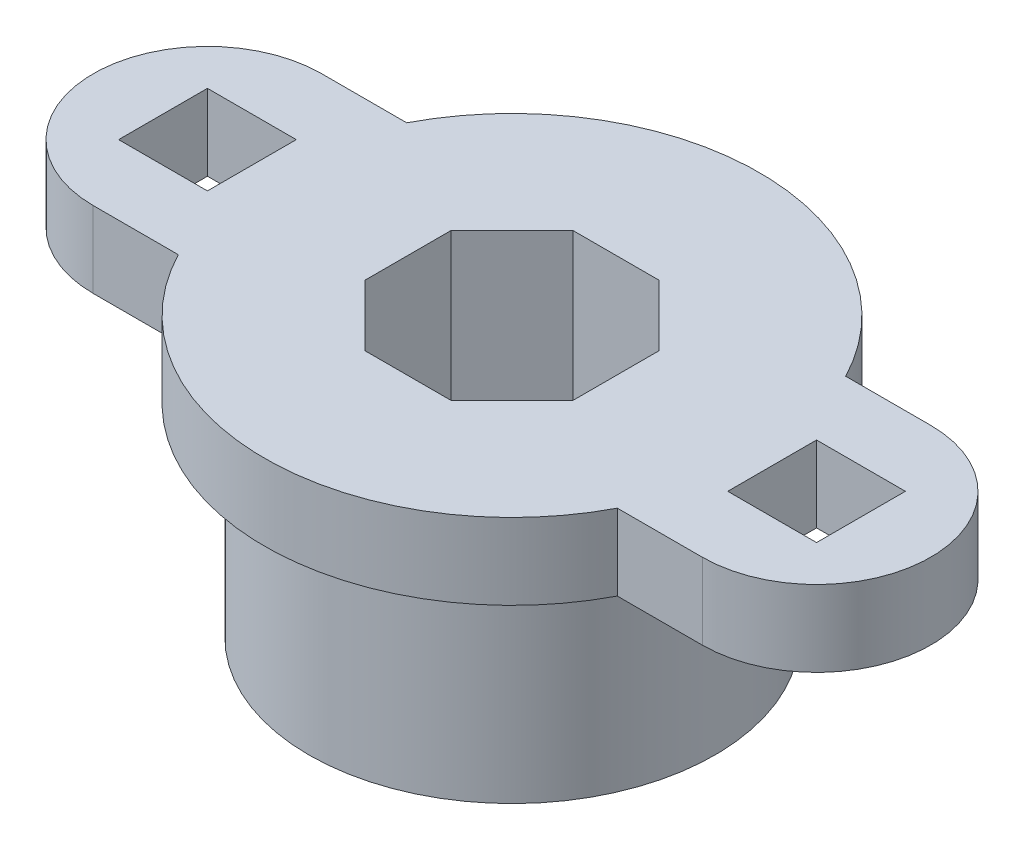
SolidWorks part; units mm, degrees
ref_plane "Front Plane" through (0, 0, 0) normal (0, 0, 1) x (1, 0, 0)
ref_plane "Top Plane" through (0, 0, 0) normal (0, 1, 0) x (1, 0, 0)
ref_plane "Right Plane" through (0, 0, 0) normal (1, 0, 0) x (0, 0, -1)
sketch "Sketch1" plane through (0, 0, 0) normal (0, 1, 0) x (1, 0, 0)
  circle A0 centre (0, 0) radius 8
  dimension "D1" = 16
extrude "Boss-Extrude1" add sketch "Sketch1" along normal blind 8
sketch "Sketch2" plane through (0, 8, 0) normal (0, 1, 0) x (1, 0, 0)
  circle A0 centre (0, 0) radius 9.75
  dimension "D1" = 19.5
extrude "Boss-Extrude2" add sketch "Sketch2" along normal blind 3
sketch "Sketch4" plane through (0, 11, 0) normal (0, 1, 0) x (1, 0, 0)
  line L0 (0, 9.75) -> (0, -9.75) construction
  line L1 (12, 0) -> (-12, 0) construction
  line L2 (12, -4.5) -> (-12, -4.5)
  line L3 (12, 4.5) -> (-12, 4.5)
  circle A0 centre (0, 0) radius 9.75 construction
  arc A1 (12, -4.5) -> (12, 4.5) centre (12, 0) ccw
  arc A2 (-12, 4.5) -> (-12, -4.5) centre (-12, 0) ccw
  point P7 (0, 0)
  dimension "D1" = 24
  dimension "D2" = 9
sketch "Sketch5" plane through (0, 11, 0) normal (0, 1, 0) x (1, 0, 0)
  line L0 (-13.75, -1.75) -> (-10.25, -1.75)
  line L1 (-10.25, -1.75) -> (-10.25, 1.75)
  line L2 (-10.25, 1.75) -> (-13.75, 1.75)
  line L3 (-13.75, 1.75) -> (-13.75, -1.75)
  line L4 (0, 9.75) -> (0, -9.75) construction
  line L5 (0, 9.75) -> (0, -9.75) construction
  line L6 (13.75, 1.75) -> (13.75, -1.75)
  line L7 (10.25, 1.75) -> (13.75, 1.75)
  line L8 (10.25, -1.75) -> (10.25, 1.75)
  line L9 (13.75, -1.75) -> (10.25, -1.75)
  circle A0 centre (-12, 0) radius 1.75 construction
  circle A1 centre (12, 0) radius 1.75 construction
  dimension "D1" = 3.5
extrude "Boss-Extrude3" add sketch "Sketch4" against normal up to surface (3 mm away) up to face at (0, 8, 9.75)
extrude "Cut-Extrude2" cut sketch "Sketch5" against normal up to next
sketch "Sketch3" plane through (0, 11, 0) normal (0, 1, 0) x (1, 0, 0)
  line L1 (4.1, 1.6983) -> (1.6983, 4.1)
  line L2 (1.6983, 4.1) -> (-1.6983, 4.1)
  line L3 (-1.6983, 4.1) -> (-4.1, 1.6983)
  line L4 (-4.1, 1.6983) -> (-4.1, -1.6983)
  line L5 (-4.1, -1.6983) -> (-1.6983, -4.1)
  line L6 (-1.6983, -4.1) -> (1.6983, -4.1)
  line L7 (1.6983, -4.1) -> (4.1, -1.6983)
  line L8 (4.1, -1.6983) -> (4.1, 1.6983)
  circle A0 centre (0, 0) radius 4.1 construction
  dimension "D1" = 8.2
extrude "Cut-Extrude1" cut sketch "Sketch3" against normal through all
